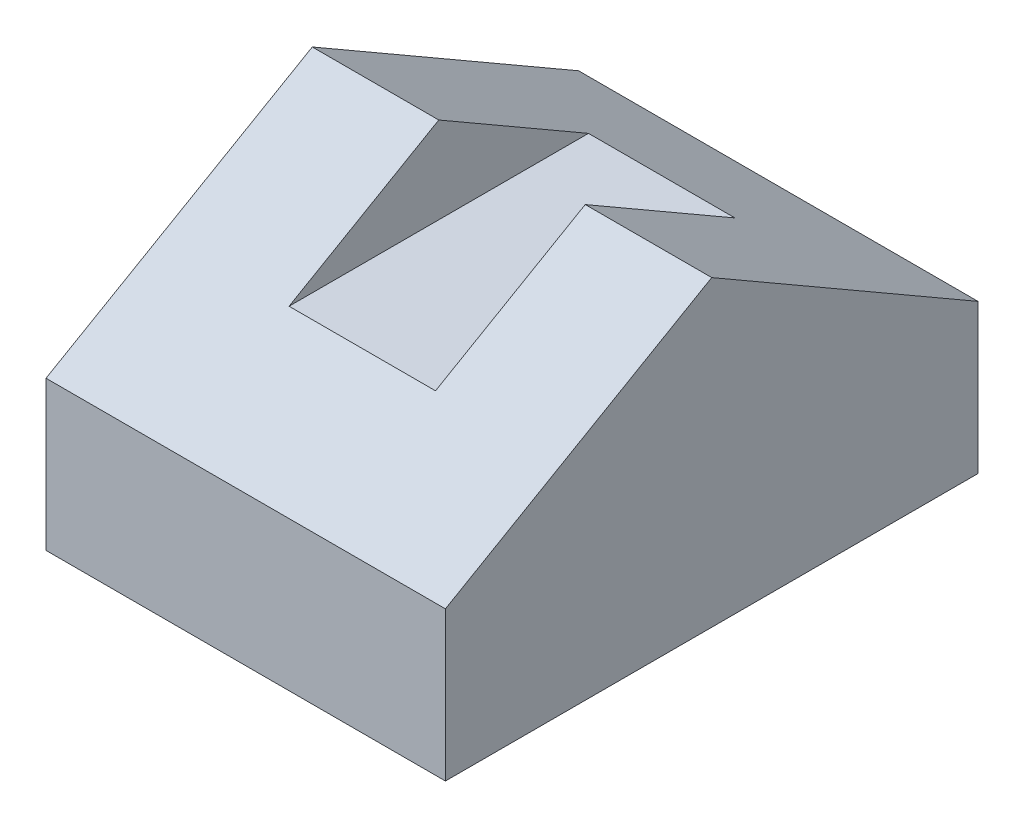
SolidWorks part; units mm, degrees
ref_plane "Front Plane" through (0, 0, 0) normal (0, 0, 1) x (1, 0, 0)
ref_plane "Top Plane" through (0, 0, 0) normal (0, 1, 0) x (1, 0, 0)
ref_plane "Right Plane" through (0, 0, 0) normal (1, 0, 0) x (0, 0, -1)
sketch "Sketch1" plane through (0, 0, 0) normal (1, 0, 0) x (0, 0, -1)
  line L1 (0.1, 0.056) -> (0, 0.1137)
  line L2 (0, 0.1137) -> (-0.1, 0.056)
  line L3 (-0.1, 0.056) -> (-0.1, 0)
  line L4 (-0.1, 0) -> (0.1, 0)
  line L5 (0.1, 0) -> (0.1, 0.056)
  point P0 (0, 0)
  point P4 (0, 0)
  dimension "D1" = 120
  dimension "D2" = 0.056
  dimension "D3" = 0.2
extrude "Boss-Extrude1" add sketch "Sketch1" along normal blind 0.15
sketch "Sketch2" plane through (0, 0, 0) normal (0, 0, 1) x (1, 0, 0)
  line L0 (0.0475, 0.1137) -> (0.1025, 0.1137)
  line L1 (0.15, 0.1137) -> (0, 0.1137) construction
  line L2 (0.0475, 0.1137) -> (0.0475, 0.0813)
  line L3 (0.0475, 0.0813) -> (0.1025, 0.0813)
  line L4 (0.1025, 0.0813) -> (0.1025, 0.1137)
  point P5 (0.075, 0.1137)
  dimension "D1" = 0.055
  dimension "D2" = 0.0325
extrude "Cut-Extrude1" cut sketch "Sketch2" against normal through all both and the other way through all
